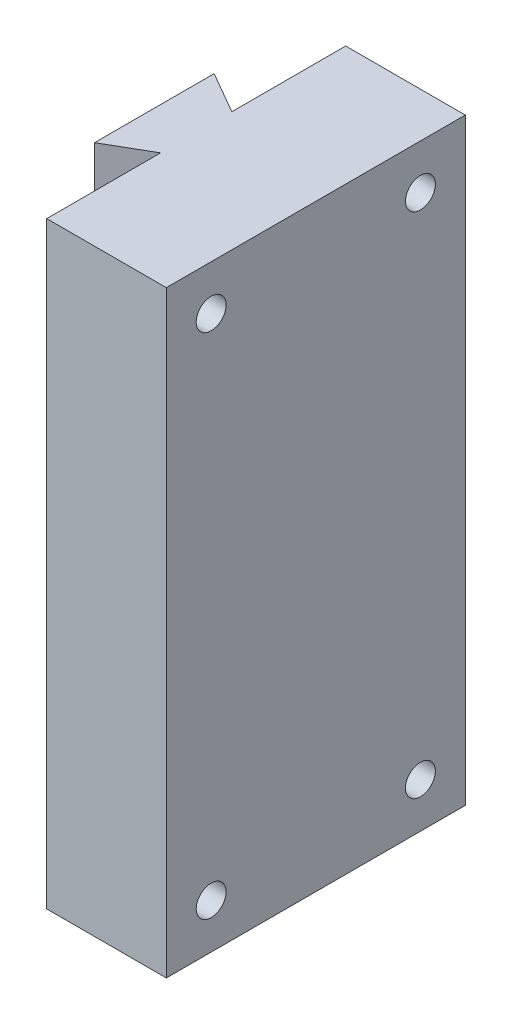
SolidWorks part; units mm, degrees
material "5052-H32"
ref_plane "Front Plane" through (0, 0, 0) normal (0, 0, 1) x (1, 0, 0)
ref_plane "Top Plane" through (0, 0, 0) normal (0, 1, 0) x (1, 0, 0)
ref_plane "Right Plane" through (0, 0, 0) normal (1, 0, 0) x (0, 0, -1)
sketch "Sketch1" plane through (0, 0, 0) normal (0, 1, 0) x (1, 0, 0)
  line L0 (-27, 10) -> (-27, -10)
  line L1 (-27, -10) -> (-20, -5.9585)
  line L2 (-20, -5.9585) -> (-20, -25)
  line L3 (-20, -25) -> (0, -25)
  line L4 (0, -25) -> (0, 25)
  line L5 (0, 25) -> (-20, 25)
  line L6 (-20, 25) -> (-20, 5.9585)
  line L7 (-20, 5.9585) -> (-27, 10)
  line L8 (-61.8655, 0) -> (80.92, 0) construction
  point P2 (0, 0)
  point P9 (-27, 0)
  dimension "D1" = 60
  dimension "D2" = 60
  dimension "D3" = 50
  dimension "D4" = 20
  dimension "D5" = 7
  dimension "D6" = 20
extrude "Boss-Extrude1" add sketch "Sketch1" along normal blind 100
sketch "Sketch2" plane through (0, 0, 0) normal (1, 0, 0) x (0, 0, -1)
  line L0 (-25, 100) -> (-25, 0) construction
  line L1 (-25, 100) -> (25, 100) construction
  line L2 (0, 103.7435) -> (0, -6.0358) construction
  line L3 (-40.2439, 50) -> (67.1156, 50) construction
  line L4 (-25, 0) -> (25, 0) construction
  circle A0 centre (-17.5, 92.5) radius 2.5
  circle A1 centre (-17.5, 7.5) radius 2.5
  circle A2 centre (17.5, 7.5) radius 2.5
  circle A3 centre (17.5, 92.5) radius 2.5
  dimension "D1" = 5
  dimension "D2" = 7.5
  dimension "D3" = 7.5
  dimension "D4" = 50
  dimension "D5" = 2
  dimension "D6" = 2
extrude "Cut-Extrude1" cut sketch "Sketch2" against normal blind 10
